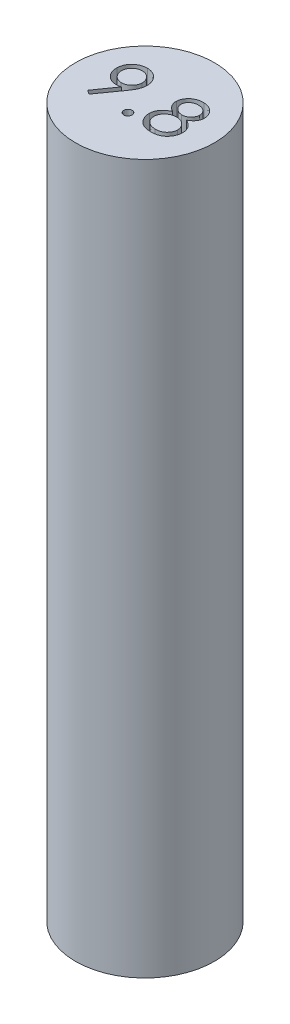
SolidWorks part; units mm, degrees
ref_plane "Front Plane" through (0, 0, 0) normal (0, 0, 1) x (1, 0, 0)
ref_plane "Top Plane" through (0, 0, 0) normal (0, 1, 0) x (1, 0, 0)
ref_plane "Right Plane" through (0, 0, 0) normal (1, 0, 0) x (0, 0, -1)
sketch "Sketch1" plane through (0, 0, 0) normal (0, 1, 0) x (1, 0, 0)
  circle A0 centre (0, 0) radius 4.9
  dimension "D1" = 9.8
extrude "Boss-Extrude1" add sketch "Sketch1" along normal blind 50
sketch "Sketch2" plane through (0, 50, 0) normal (0, 1, 0) x (1, 0, 0)
  line L0 (-4.49, -1.3062) -> (4.3229, -1.5557) construction
  text T0 "9.8"
extrude "Cut-Extrude1" cut sketch "Sketch2" against normal blind 3
